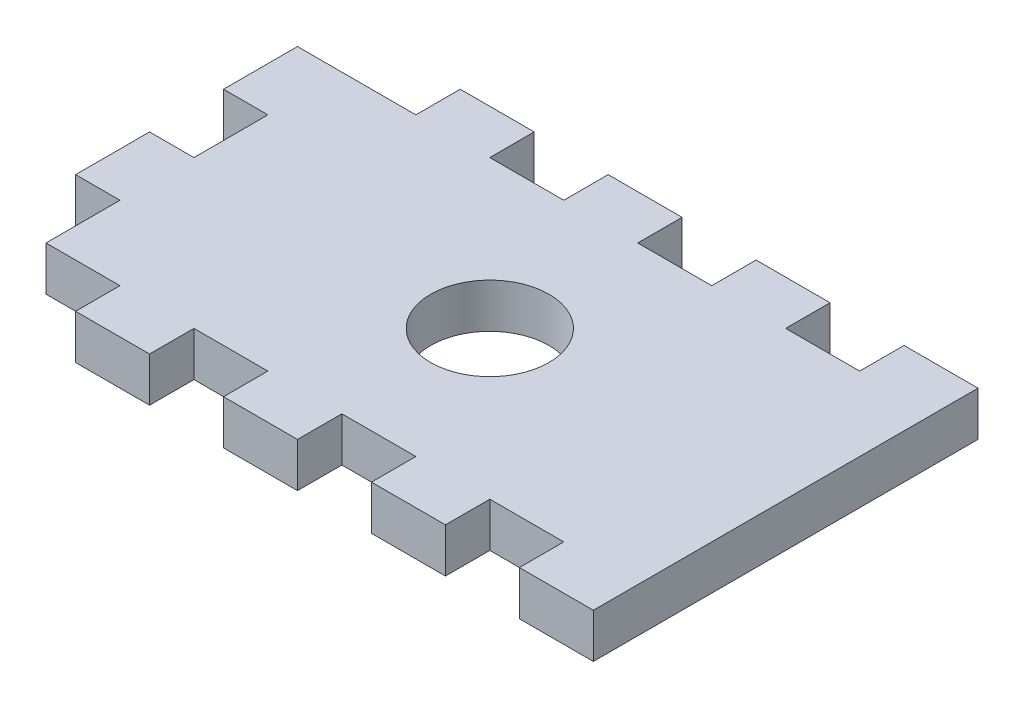
SolidWorks part; units mm, degrees
ref_plane "Front Plane" through (0, 0, 0) normal (0, 0, 1) x (1, 0, 0)
ref_plane "Top Plane" through (0, 0, 0) normal (0, 1, 0) x (1, 0, 0)
ref_plane "Right Plane" through (0, 0, 0) normal (1, 0, 0) x (0, 0, -1)
sketch "Sketch1" plane through (0, 0, 0) normal (0, 1, 0) x (1, 0, 0)
  line L1 (-20, 13) -> (20, 13)
  line L2 (-20, 13) -> (-20, -13)
  line L3 (-20, -13) -> (20, -13)
  line L4 (20, 13) -> (20, -13)
  line L5 (-20, 13) -> (20, -13) construction
  line L6 (-20, -13) -> (20, 13) construction
  point P0 (0, 0)
  dimension "D1" = 40
  dimension "D2" = 26
extrude "Boss-Extrude1" add sketch "Sketch1" along normal mid plane 3
sketch "Sketch2" plane through (0, -1.5, 0) normal (0, -1, 0) x (1, 0, 0)
  circle A0 centre (0, 0) radius 4
  dimension "D1" = 8
extrude "Cut-Extrude1" cut sketch "Sketch2" against normal up to surface (3 mm away) up to face at (0, 1.5, 0)
sketch "Sketch8" plane through (-20, 0, 0) normal (-1, 0, 0) x (0, 0, 1)
  line L0 (-13, -1.5) -> (13, -1.5) construction
  line L1 (-13, 1.5) -> (-10, 1.5)
  line L2 (-13, 1.5) -> (-13, -1.5)
  line L3 (-13, -1.5) -> (-10, -1.5)
  line L4 (-10, 1.5) -> (-10, -1.5)
  line L6 (13, 1.5) -> (10, 1.5)
  line L7 (13, 1.5) -> (13, -1.5)
  line L8 (13, -1.5) -> (10, -1.5)
  line L9 (10, 1.5) -> (10, -1.5)
  line L10 (-10, 1.5) -> (-5, 1.5)
  line L11 (-10, 1.5) -> (-10, -1.5)
  line L12 (-10, -1.5) -> (-5, -1.5)
  line L13 (-5, 1.5) -> (-5, -1.5)
  line L18 (5, 1.5) -> (10, 1.5)
  line L19 (5, 1.5) -> (5, -1.5)
  line L20 (5, -1.5) -> (10, -1.5)
  line L21 (10, 1.5) -> (10, -1.5)
  line L22 (-5, 1.5) -> (0, 1.5)
  line L23 (-5, 1.5) -> (-5, -1.5)
  line L24 (-5, -1.5) -> (0, -1.5)
  line L25 (0, 1.5) -> (0, -1.5)
  line L26 (0, 1.5) -> (5, 1.5)
  line L27 (0, 1.5) -> (0, -1.5)
  line L28 (0, -1.5) -> (5, -1.5)
  line L29 (5, 1.5) -> (5, -1.5)
  line M12 (-13, -1.5) -> (13, -1.5)
  line M14 (13, 1.5) -> (-13, 1.5)
  dimension "D1" = 3
extrude "Boss-Extrude7" add sketch "Sketch8" along normal blind 3 contours L13 L4 M14 M12 | L25 L19 M14 M12
sketch "Sketch9" plane through (0, -1.5, 0) normal (0, -1, 0) x (1, 0, 0)
  line L0 (-23, -10) -> (-20, -10) construction
  line L1 (-20, -13) -> (-15, -13)
  line L2 (-20, -13) -> (-20, -10)
  line L3 (-20, -10) -> (-15, -10)
  line L4 (-15, -13) -> (-15, -10)
  line L5 (0, 0) -> (-5.3473, 0) construction
  line L6 (-15, -13) -> (-10, -13)
  line L7 (-15, -13) -> (-15, -10)
  line L8 (-15, -10) -> (-10, -10)
  line L9 (-10, -13) -> (-10, -10)
  line L10 (-10, -13) -> (-5, -13)
  line L11 (-10, -13) -> (-10, -10)
  line L12 (-10, -10) -> (-5, -10)
  line L13 (-5, -13) -> (-5, -10)
  line L14 (-10, 10) -> (-5, 10)
  line L15 (-5, 13) -> (-5, 10)
  line L16 (-10, 13) -> (-5, 13)
  line L17 (-10, 13) -> (-10, 10)
  line L18 (-15, 10) -> (-10, 10)
  line L19 (-10, 13) -> (-10, 10)
  line L20 (-15, 13) -> (-10, 13)
  line L21 (-15, 13) -> (-15, 10)
  line L22 (-20, 10) -> (-15, 10)
  line L23 (-15, 13) -> (-15, 10)
  line L24 (-20, 13) -> (-15, 13)
  line L25 (-20, 13) -> (-20, 10)
  line L26 (15, 10) -> (20, 10)
  line L27 (-5, -13) -> (0, -13)
  line L28 (-5, -13) -> (-5, -10)
  line L29 (-5, -10) -> (0, -10)
  line L30 (0, -13) -> (0, -10)
  line L31 (0, -13) -> (5, -13)
  line L32 (0, -13) -> (0, -10)
  line L33 (0, -10) -> (5, -10)
  line L34 (5, -13) -> (5, -10)
  line L35 (5, -13) -> (10, -13)
  line L36 (5, -13) -> (5, -10)
  line L37 (5, -10) -> (10, -10)
  line L38 (10, -13) -> (10, -10)
  line L39 (10, -13) -> (15, -13)
  line L40 (10, -13) -> (10, -10)
  line L41 (10, -10) -> (15, -10)
  line L42 (15, -13) -> (15, -10)
  line L43 (15, -13) -> (20, -13)
  line L44 (15, -13) -> (15, -10)
  line L45 (15, -10) -> (20, -10)
  line L46 (20, -13) -> (20, -10)
  line L47 (20, 13) -> (20, 10)
  line L48 (15, 13) -> (20, 13)
  line L49 (15, 13) -> (15, 10)
  line L50 (10, 10) -> (15, 10)
  line L51 (15, 13) -> (15, 10)
  line L52 (10, 13) -> (15, 13)
  line L53 (10, 13) -> (10, 10)
  line L54 (5, 10) -> (10, 10)
  line L55 (10, 13) -> (10, 10)
  line L56 (5, 13) -> (10, 13)
  line L57 (5, 13) -> (5, 10)
  line L58 (0, 10) -> (5, 10)
  line L59 (5, 13) -> (5, 10)
  line L60 (0, 13) -> (5, 13)
  line L61 (0, 13) -> (0, 10)
  line L62 (-5, 10) -> (0, 10)
  line L63 (0, 13) -> (0, 10)
  line L64 (-5, 13) -> (0, 13)
  line L65 (-5, 13) -> (-5, 10)
  line M11 (20, 13) -> (-20, 13)
  line M12 (-20, 13) -> (-20, 5)
  line M20 (-20, -10) -> (-20, -13)
  line M21 (-20, -13) -> (20, -13)
  dimension "D1" = 5
extrude "Cut-Extrude2" cut sketch "Sketch9" against normal up to surface (3 mm away) contours L4 L3 M21 M20 | L13 L12 L9 M21 | L22 L21 M12 M11 | L17 L14 L15 M11 | L61 L58 L57 M11 | L53 L50 L49 M11 | L32 L31 L34 L33 | L40 L39 L42 L41
